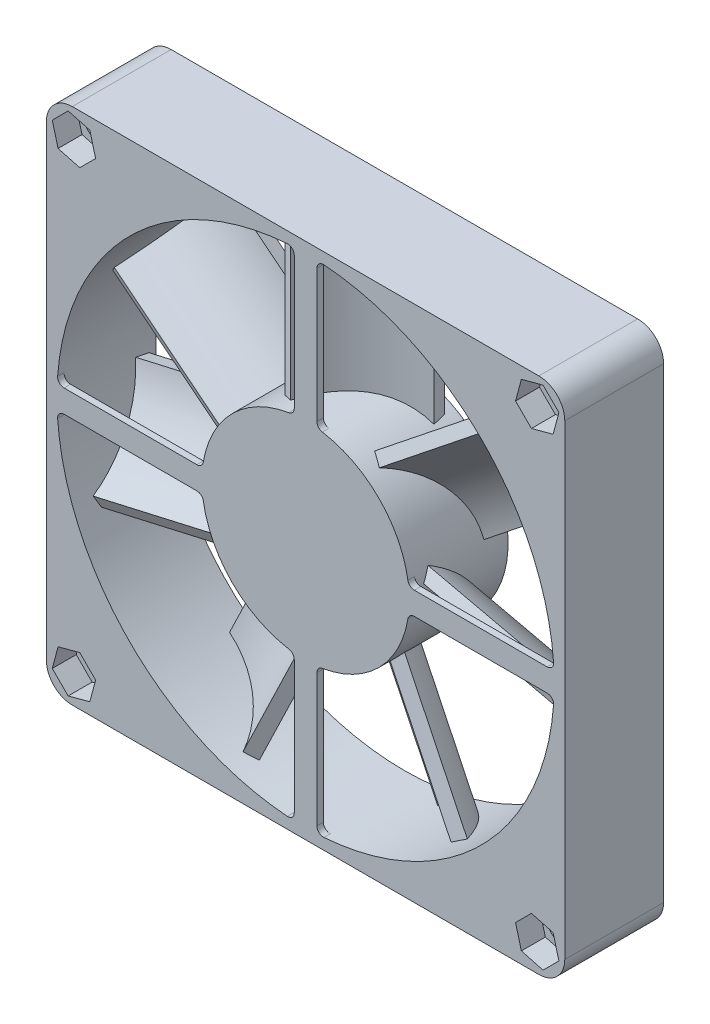
SolidWorks part; units mm, degrees
ref_plane "Front Plane" through (0, 0, 0) normal (0, 0, 1) x (1, 0, 0)
ref_plane "Top Plane" through (0, 0, 0) normal (0, 1, 0) x (1, 0, 0)
ref_plane "Right Plane" through (0, 0, 0) normal (1, 0, 0) x (0, 0, -1)
sketch "Sketch1" plane through (0, 0, 0) normal (0, 0, 1) x (1, 0, 0)
  line L0 (-35.75, 35.75) -> (35.75, -35.75) construction
  line L1 (-36, 40) -> (36, 40)
  line L2 (-40, 36) -> (-40, -36)
  line L3 (-36, -40) -> (36, -40)
  line L4 (40, 36) -> (40, -36)
  line L5 (-40, 0) -> (0, 0) construction
  line L6 (0, 0) -> (0, 40) construction
  circle A0 centre (0, 0) radius 38.375
  circle A1 centre (-35.75, 35.75) radius 2.11
  circle A2 centre (-35.75, -35.75) radius 2.11
  circle A3 centre (35.75, -35.75) radius 2.11
  circle A4 centre (35.75, 35.75) radius 2.11
  arc A5 (36, 40) -> (40, 36) centre (36, 36) cw
  arc A6 (36, -40) -> (40, -36) centre (36, -36) ccw
  arc A7 (-40, -36) -> (-36, -40) centre (-36, -36) ccw
  arc A8 (-36, 40) -> (-40, 36) centre (-36, 36) ccw
  dimension "D1" = 4
  dimension "D4" = 76.75
  dimension "D5" = 4.22
  dimension "D2" = 80
  dimension "D3" = 71.5
  dimension "D6" = 71.5
extrude "Boss-Extrude1" add sketch "Sketch1" along normal blind 15.25
sketch "Sketch2" plane through (0, 0, 15.25) normal (0, 0, 1) x (1, 0, 0)
  line L0 (-1.75, 37.2737) -> (-1.75, 16.7761)
  line L1 (1.75, 37.2737) -> (1.75, 16.7761)
  line L2 (-1.75, 27.0249) -> (1.75, 27.0249) construction
  line L3 (0, 27.0249) -> (0, 0) construction
  arc A0 (-2.5882, 15.7893) -> (2.5882, 15.7893) centre (0, 0) ccw
  circle A1 centre (0, 0) radius 38.375 construction
  arc A2 (2.8236, 38.271) -> (-2.8236, 38.271) centre (0, 0) ccw
  arc A3 (1.75, 16.7761) -> (2.5882, 15.7893) centre (2.75, 16.7761) ccw
  arc A4 (2.8236, 38.271) -> (1.75, 37.2737) centre (2.75, 37.2737) ccw
  arc A5 (-1.75, 37.2737) -> (-2.8236, 38.271) centre (-2.75, 37.2737) ccw
  arc A6 (-1.75, 16.7761) -> (-2.5882, 15.7893) centre (-2.75, 16.7761) cw
  dimension "D1" = 32
  dimension "D2" = 1
  dimension "D3" = 3.5
extrude "Boss-Extrude2" add sketch "Sketch2" against normal blind 1
pattern_circular "CirPattern1" count 4 over 360 about axis through (0, 0, 0) along (0, 0, 1) of "Boss-Extrude2"
sketch "Sketch4" plane through (0, 0, 14.25) normal (0, 0, -1) x (-1, 0, 0)
  circle A0 centre (0, 0) radius 16
extrude "Boss-Extrude3" add sketch "Sketch4" along normal up to surface (14.25 mm away) up to face at (37.86, -35.75, 0)
sketch "Sketch5" plane through (0, 0, 0) normal (0, 1, 0) x (1, 0, 0)
  arc A0 (-6.3783, -12.0873) -> (7.8145, -1.6116) centre (11.1464, -20.9781) cw
extrude "Extrude-Thin1" add sketch "Sketch5" along normal blind 37 thin
pattern_circular "CirPattern2" count 7 over 360 about axis through (0, 0, 0) along (0, 0, 1) of "Extrude-Thin1"
sketch "Sketch6" plane through (0, 0, 0) normal (0, 0, -1) x (-1, 0, 0)
  line L0 (-35.75, 35.75) -> (0, 0) construction
  line L1 (-36.6466, 39.0961) -> (-39.0961, 36.6466)
  line L2 (-39.0961, 36.6466) -> (-38.1995, 33.3005)
  line L3 (-38.1995, 33.3005) -> (-34.8534, 32.4039)
  line L4 (-34.8534, 32.4039) -> (-32.4039, 34.8534)
  line L5 (-32.4039, 34.8534) -> (-33.3005, 38.1995)
  line L6 (-33.3005, 38.1995) -> (-36.6466, 39.0961)
  circle A0 centre (-35.75, 35.75) radius 3 construction
  dimension "D1" = 6
extrude "Cut-Extrude1" cut sketch "Sketch6" against normal blind 3.7
sketch "Sketch7" plane through (0, 0, 15.25) normal (0, 0, 1) x (1, 0, 0)
  line L6 (36.6466, 39.0961) -> (33.3005, 38.1995)
  line L7 (39.0961, 36.6466) -> (36.6466, 39.0961)
  line L8 (38.1995, 33.3005) -> (39.0961, 36.6466)
  line L9 (34.8534, 32.4039) -> (38.1995, 33.3005)
  line L10 (32.4039, 34.8534) -> (34.8534, 32.4039)
  line L11 (33.3005, 38.1995) -> (32.4039, 34.8534)
  line L12 (36.6466, 39.0961) -> (33.3005, 38.1995)
  line L13 (39.0961, 36.6466) -> (36.6466, 39.0961)
  line L14 (38.1995, 33.3005) -> (39.0961, 36.6466)
  line L15 (34.8534, 32.4039) -> (38.1995, 33.3005)
  line L16 (32.4039, 34.8534) -> (34.8534, 32.4039)
  line L17 (33.3005, 38.1995) -> (32.4039, 34.8534)
  dimension "D1" = 0
extrude "Cut-Extrude2" cut sketch "Sketch7" against normal blind 3.7
pattern_circular "CirPattern3" count 4 over 360 about axis through (0, 0, 0) along (0, 0, 1) of "Cut-Extrude2", "Cut-Extrude1"
